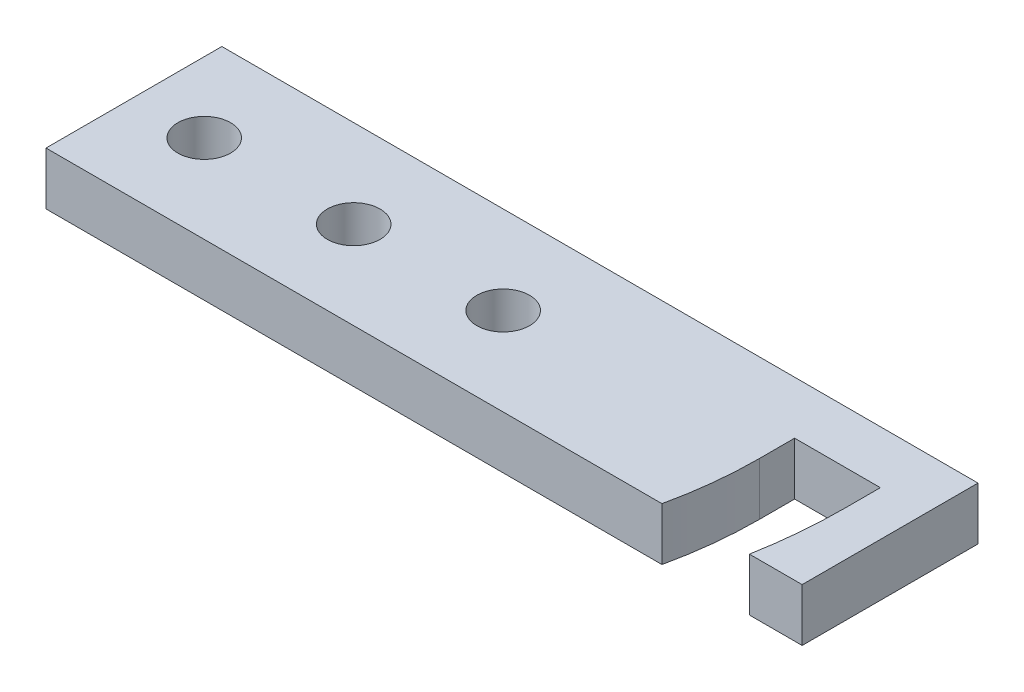
SolidWorks part; units mm, degrees
ref_plane "Plan de face" through (0, 0, 0) normal (0, 0, 1) x (1, 0, 0)
ref_plane "Plan de dessus" through (0, 0, 0) normal (0, 1, 0) x (1, 0, 0)
ref_plane "Plan de droite" through (0, 0, 0) normal (1, 0, 0) x (0, 0, -1)
sketch "Esquisse1" plane through (0, 0, 0) normal (0, 1, 0) x (1, 0, 0)
  line L0 (36.5, 0) -> (36.5, 2.8203)
  line L1 (0, 0) -> (43, 0)
  line L2 (0, 0) -> (0, 10)
  line L3 (0, 10) -> (43, 10)
  line L4 (43, 0) -> (43, 10)
  line L5 (36.5, 2.8203) -> (40, 2.8203)
  line L6 (40, 2.8203) -> (40, 0)
  circle A0 centre (4, 4.9973) radius 1.5
  circle A1 centre (12.5, 4.9973) radius 1.5
  circle A2 centre (21, 4.9973) radius 1.5
  point P17 (14.9021, 4.0445)
  dimension "D3" = 3
  dimension "D4" = 3
  dimension "D5" = 3
  dimension "D1" = 43
  dimension "D2" = 10
  dimension "D6" = 8.5
  dimension "D7" = 0
  dimension "D8" = 8.5
  dimension "D9" = 3.5
  dimension "D10" = 3
  dimension "D11" = 4
extrude "Boss.-Extru.2" add sketch "Esquisse1" along normal blind 3 contours L5 L6 L1 L4 L3 L2 L0 A2 A1 A0
sketch "Esquisse2" plane through (0, 3, 0) normal (0, 1, 0) x (1, 0, 0)
  line L0 (35.6028, 4.9973) -> (40.4504, 4.9973)
  line L1 (40, 0) -> (40, 2.8203)
  line L2 (40, 2.8203) -> (36.5, 2.8203)
  line L3 (0, 0) -> (36.5, 0) construction
  line L4 (35.0271, 0) -> (36.5, 0)
  line L5 (36.5, 0) -> (36.5, 2.8203)
  line L6 (36.5, 2.8203) -> (35.4684, 2.829)
  line L7 (35.6028, 4.9973) -> (35.5747, 4.9973)
  arc A0 (35.0271, 0) -> (35.5747, 4.9973) centre (12.5, 4.9973) ccw
  arc A1 (40, 0) -> (40.4504, 4.9973) centre (12.5, 4.9973) ccw
  line M9 (36.5, 2.8203) -> (40, 2.8203)
  line M10 (40, 2.8203) -> (40, 0)
extrude "Enlèv. mat.-Extru.2" cut sketch "Esquisse2" against normal blind 3 contours A1 L0 L7 A0 L6 M10 M9
sketch "Esquisse3" plane through (0, 3, 0) normal (0, 1, 0) x (1, 0, 0)
  line L0 (35.5747, 4.9973) -> (35.5747, 6.9973)
  line L1 (35.5747, 6.9973) -> (40.4504, 6.9973)
  line L2 (40.4504, 6.9973) -> (40.4504, 4.9973)
  line L3 (40.4504, 4.9973) -> (35.5747, 4.9973)
  dimension "D1" = 2
extrude "Enlèv. mat.-Extru.3" cut sketch "Esquisse3" against normal blind 3
